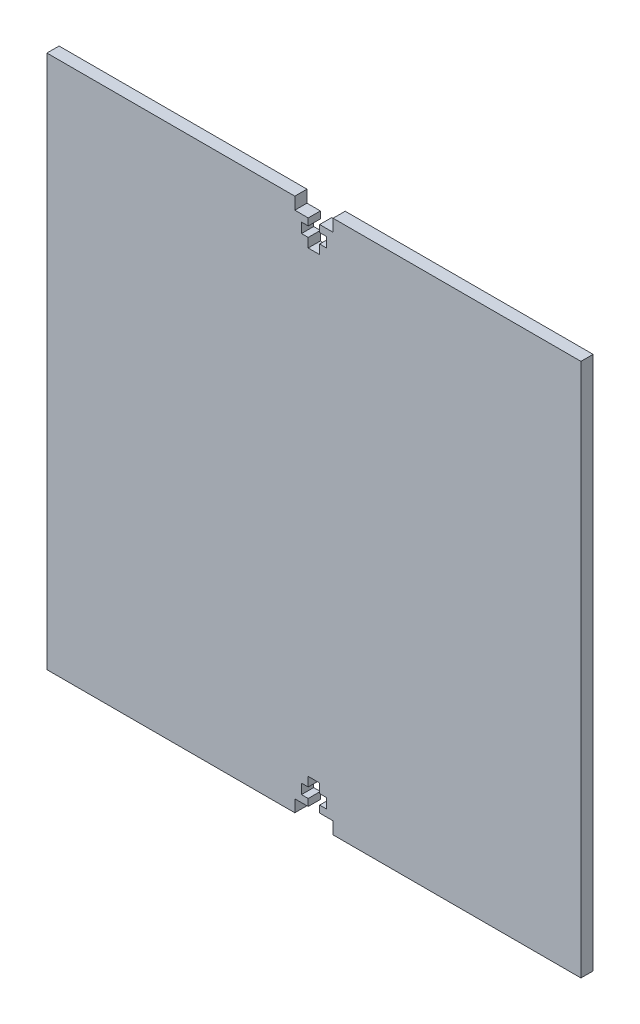
SolidWorks part; units mm, degrees
ref_plane "Front Plane" through (0, 0, 0) normal (0, 0, 1) x (1, 0, 0)
ref_plane "Top Plane" through (0, 0, 0) normal (0, 1, 0) x (1, 0, 0)
ref_plane "Right Plane" through (0, 0, 0) normal (1, 0, 0) x (0, 0, -1)
sketch "Sketch1" plane through (0, 0, 0) normal (0, 0, 1) x (1, 0, 0)
  line L1 (-69.85, 69.85) -> (69.85, 69.85)
  line L2 (-69.85, 69.85) -> (-69.85, -69.85)
  line L3 (-69.85, -69.85) -> (69.85, -69.85)
  line L4 (69.85, 69.85) -> (69.85, -69.85)
  line L5 (-69.85, 69.85) -> (69.85, -69.85) construction
  line L6 (-69.85, -69.85) -> (69.85, 69.85) construction
  point P0 (0, 0)
  dimension "D1" = 139.7
  dimension "D2" = 139.7
extrude "Boss-Extrude1" add sketch "Sketch1" along normal blind 3.18
sketch "Sketch2" plane through (-8.5645, 11.1672, 0) normal (0, 0, -1) x (-1, 0, 0)
  line L0 (-8.5645, 58.6828) -> (-8.5645, 48.6828) construction
  line L1 (61.2855, 58.6828) -> (-78.4145, 58.6828) construction
  line L2 (-7.0645, 55.5028) -> (-3.5645, 55.5028)
  line L3 (-13.5645, 58.6828) -> (-3.5645, 58.6828)
  line L4 (-13.5645, 58.6828) -> (-13.5645, 55.5028)
  line L5 (-13.5645, 55.5028) -> (-10.0645, 55.5028)
  line L6 (-3.5645, 58.6828) -> (-3.5645, 55.5028)
  line L8 (-10.0645, 55.5028) -> (-10.0645, 53.6828)
  line L9 (-10.0645, 48.6828) -> (-7.0645, 48.6828)
  line L10 (-7.0645, 55.5028) -> (-7.0645, 53.6828)
  line L11 (-11.8145, 53.6828) -> (-5.3145, 53.6828) construction
  line L12 (-11.8145, 53.6828) -> (-11.8145, 51.0828)
  line L13 (-11.8145, 51.0828) -> (-10.0645, 51.0828)
  line L14 (-5.3145, 53.6828) -> (-5.3145, 51.0828)
  line L15 (-10.0645, 51.0828) -> (-10.0645, 48.6828)
  line L16 (-7.0645, 51.0828) -> (-5.3145, 51.0828)
  line L17 (-7.0645, 51.0828) -> (-7.0645, 48.6828)
  line L18 (-11.8145, 53.6828) -> (-10.0645, 53.6828)
  line L19 (-5.3145, 53.6828) -> (-7.0645, 53.6828)
  point P17 (-8.5645, 53.6828)
  dimension "D1" = 3.18
  dimension "D2" = 10
  dimension "D3" = 3
  dimension "D4" = 2.6
  dimension "D5" = 6.5
  dimension "D6" = 10
extrude "Cut-Extrude1" cut sketch "Sketch2" against normal through all
other "TholeCutmkIVtru<1>"
sketch "Sketch23" plane through (17.6653, -90.0638, 3.18) normal (0, 0, 1) x (1, 0, 0)
  line L0 (-17.6653, 20.2138) -> (-17.6653, 30.2138) construction
  line L1 (-87.5153, 20.2138) -> (52.1847, 20.2138) construction
  line L2 (-19.1653, 23.3938) -> (-22.6653, 23.3938)
  line L3 (-12.6653, 20.2138) -> (-22.6653, 20.2138)
  line L4 (-12.6653, 20.2138) -> (-12.6653, 23.3938)
  line L5 (-12.6653, 23.3938) -> (-16.1653, 23.3938)
  line L6 (-22.6653, 20.2138) -> (-22.6653, 23.3938)
  line L8 (-16.1653, 23.3938) -> (-16.1653, 25.2138)
  line L9 (-16.1653, 30.2138) -> (-19.1653, 30.2138)
  line L10 (-19.1653, 23.3938) -> (-19.1653, 25.2138)
  line L11 (-14.4153, 25.2138) -> (-20.9153, 25.2138) construction
  line L12 (-14.4153, 25.2138) -> (-14.4153, 27.8138)
  line L13 (-14.4153, 27.8138) -> (-16.1653, 27.8138)
  line L14 (-20.9153, 25.2138) -> (-20.9153, 27.8138)
  line L15 (-16.1653, 27.8138) -> (-16.1653, 30.2138)
  line L16 (-19.1653, 27.8138) -> (-20.9153, 27.8138)
  line L17 (-19.1653, 27.8138) -> (-19.1653, 30.2138)
  line L18 (-14.4153, 25.2138) -> (-16.1653, 25.2138)
  line L19 (-20.9153, 25.2138) -> (-19.1653, 25.2138)
  line L20 (52.1847, 20.2138) -> (52.1847, 159.9138) construction
  point P17 (-17.6653, 25.2138)
  dimension "D1" = 3.18
  dimension "D2" = 10
  dimension "D3" = 3
  dimension "D4" = 2.6
  dimension "D5" = 6.5
  dimension "D6" = 10
extrude "Cut-Extrude13" cut sketch "Sketch23" against normal through all
other "TholeCutmkVtru<1>"
